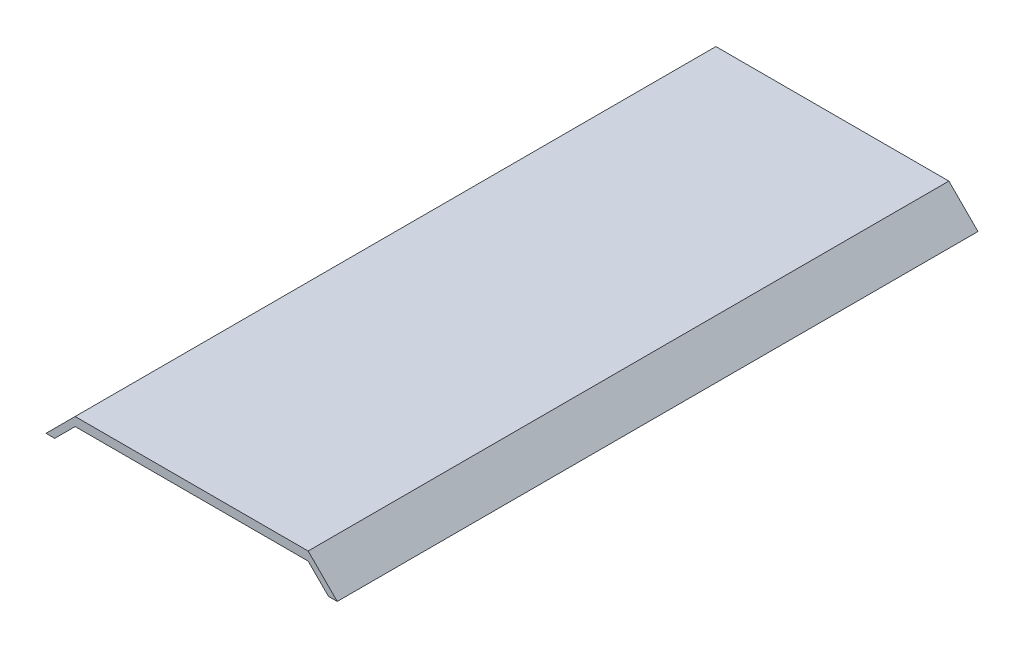
SolidWorks part; units mm, degrees
ref_plane "Alzado" through (0, 0, 0) normal (0, 0, 1) x (1, 0, 0)
ref_plane "Planta" through (0, 0, 0) normal (0, 1, 0) x (1, 0, 0)
ref_plane "Vista lateral" through (0, 0, 0) normal (1, 0, 0) x (0, 0, -1)
sketch "Croquis1" plane through (0, 0, 0) normal (0, 0, 1) x (1, 0, 0)
  line L0 (-47, 0) -> (47, 0) construction
  line L1 (-47, 0) -> (-50, 0)
  line L2 (47, 0) -> (50, 0)
  line L3 (-47, 0) -> (-40, 7)
  line L4 (-40, 7) -> (40, 7)
  line L5 (40, 7) -> (47, 0)
  line L6 (-50, 0) -> (-40, 10)
  line L7 (-40, 10) -> (40, 10)
  line L8 (40, 10) -> (50, 0)
  point P4 (0, 0)
  dimension "D1" = 94
  dimension "D2" = 3
  dimension "D3" = 135
  dimension "D4" = 135
  dimension "D5" = 7
  dimension "D6" = 3
extrude "Saliente-Extruir1" add sketch "Croquis1" along normal blind 220
